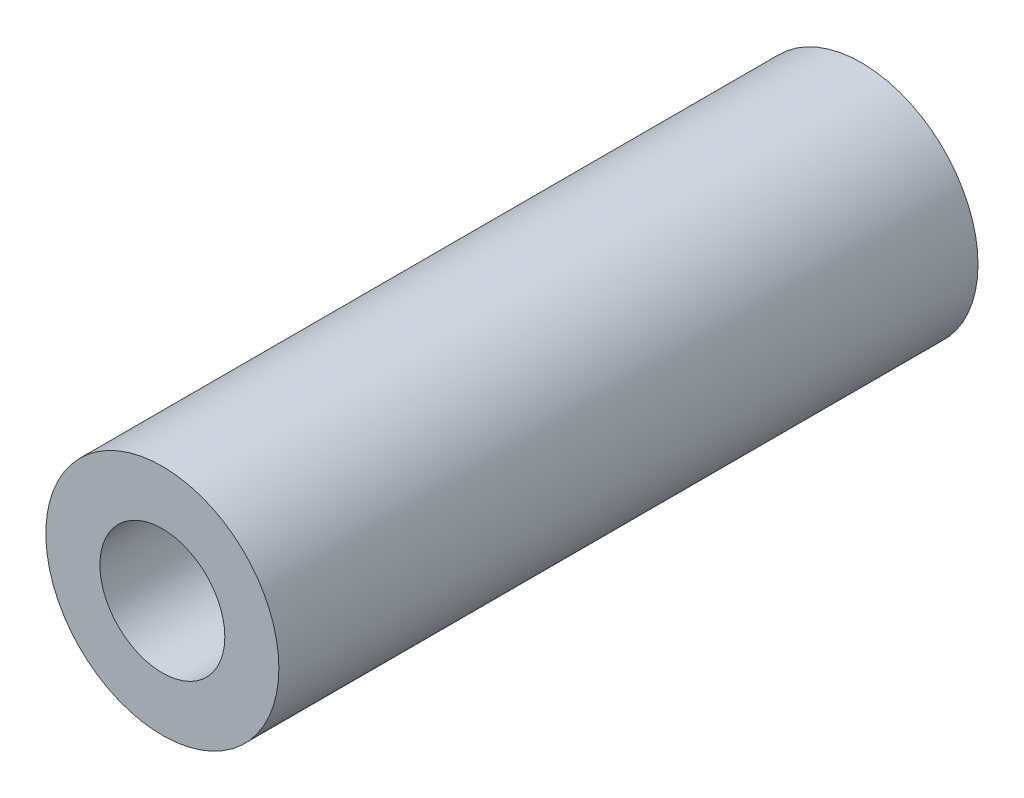
SolidWorks part; units mm, degrees
ref_plane "Front Plane" through (0, 0, 0) normal (0, 0, 1) x (1, 0, 0)
ref_plane "Top Plane" through (0, 0, 0) normal (0, 1, 0) x (1, 0, 0)
ref_plane "Right Plane" through (0, 0, 0) normal (1, 0, 0) x (0, 0, -1)
sketch "Sketch1" plane through (0, 0, 0) normal (0, 0, 1) x (1, 0, 0)
  circle A0 centre (0, 0) radius 4.7625
  circle A1 centre (0, 0) radius 2.5527
  dimension "D1" = 5.1054
  dimension "D2" = 9.525
extrude "Boss-Extrude1" add sketch "Sketch1" along normal blind 28.575
